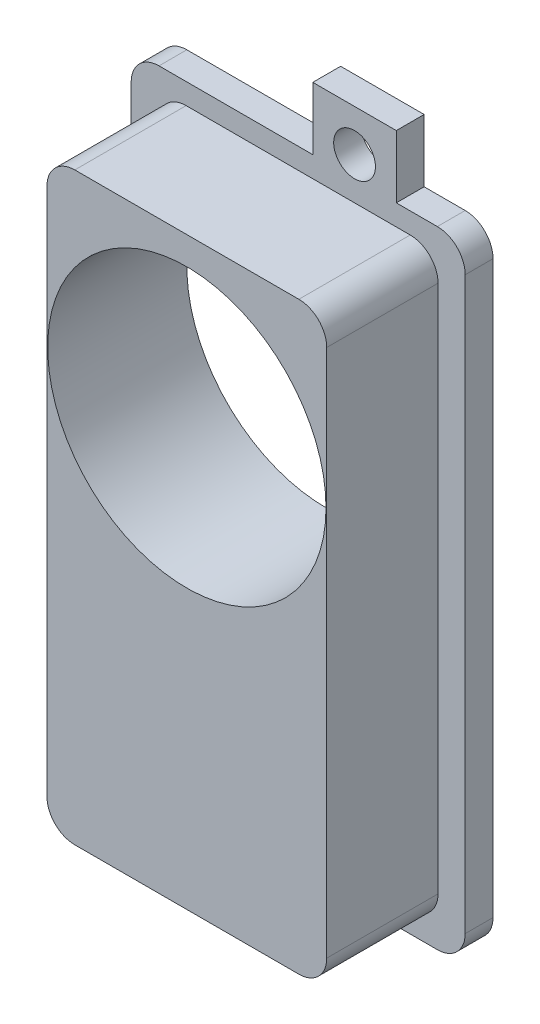
SolidWorks part; units mm, degrees
ref_plane "Front Plane" through (0, 0, 0) normal (0, 0, 1) x (1, 0, 0)
ref_plane "Top Plane" through (0, 0, 0) normal (0, 1, 0) x (1, 0, 0)
ref_plane "Right Plane" through (0, 0, 0) normal (1, 0, 0) x (0, 0, -1)
sketch "Sketch1" plane through (0, 0, 0) normal (0, 0, 1) x (1, 0, 0)
  line L0 (1.05, 22.5) -> (1.05, 27)
  line L1 (12, -22.5) -> (-1.05, -22.5)
  line L2 (12, -22.5) -> (12, 22.5)
  line L3 (12, 22.5) -> (7.05, 22.5)
  line L4 (-12, -22.5) -> (-12, 22.5)
  line L5 (12, -22.5) -> (-12, 22.5) construction
  line L6 (12, 22.5) -> (-12, -22.5) construction
  line L7 (1.05, 27) -> (7.05, 27)
  line L8 (7.05, 27) -> (7.05, 22.5)
  line L9 (1.05, 22.5) -> (-12, 22.5)
  line L10 (-12, 0) -> (12, 0) construction
  line L11 (-1.05, -27) -> (-1.05, -22.5)
  line L12 (-7.05, -27) -> (-1.05, -27)
  line L13 (-7.05, -22.5) -> (-7.05, -27)
  line L14 (-7.05, -22.5) -> (-12, -22.5)
  circle A0 centre (4.05, 24) radius 1.5
  circle A1 centre (-4.05, -24) radius 1.5
  point P0 (0, 0)
  point P22 (-4.8748, -23.8471)
  dimension "D6" = 3
  dimension "D12" = 3
  dimension "D1" = 45
  dimension "D2" = 24
  dimension "D3" = 13.05
  dimension "D4" = 6
  dimension "D5" = 4.5
  dimension "D7" = 3
  dimension "D8" = 1.5
  dimension "D9" = 6
  dimension "D10" = 13.05
  dimension "D11" = 4.5
  dimension "D13" = 3
  dimension "D14" = 1.5
extrude "Boss-Extrude1" add sketch "Sketch1" along normal blind 2
fillet "Fillet1" radius 2 4 edges at (12, -22.5, 1) (-12, -22.5, 1) (-12, 22.5, 1) (12, 22.5, 1)
sketch "Sketch3" plane through (0, 0, 2) normal (0, 0, 1) x (1, 0, 0)
  line L0 (1.05, 22.5) -> (-10, 22.5) construction
  line L1 (10.05, -21) -> (-10.05, -21)
  line L2 (10.05, -21) -> (10.05, 21)
  line L3 (10.05, 21) -> (-10.05, 21)
  line L4 (-10.05, -21) -> (-10.05, 21)
  line L5 (10.05, -21) -> (-10.05, 21) construction
  line L6 (10.05, 21) -> (-10.05, -21) construction
  point P0 (0, 0)
  dimension "D1" = 1.5
  dimension "D2" = 20.1
extrude "Boss-Extrude2" add sketch "Sketch3" along normal blind 8
fillet "Fillet2" radius 2 4 edges at (10.05, 21, 6) (10.05, -21, 6) (-10.05, -21, 6) (-10.05, 21, 6)
sketch "Sketch5" plane through (0, 0, 10) normal (0, 0, 1) x (1, 0, 0)
  line L0 (8.05, 21) -> (-8.05, 21) construction
  circle A0 centre (0, 9) radius 10
  dimension "D1" = 20
  dimension "D2" = 12
extrude "Cut-Extrude3" cut sketch "Sketch5" against normal through all
